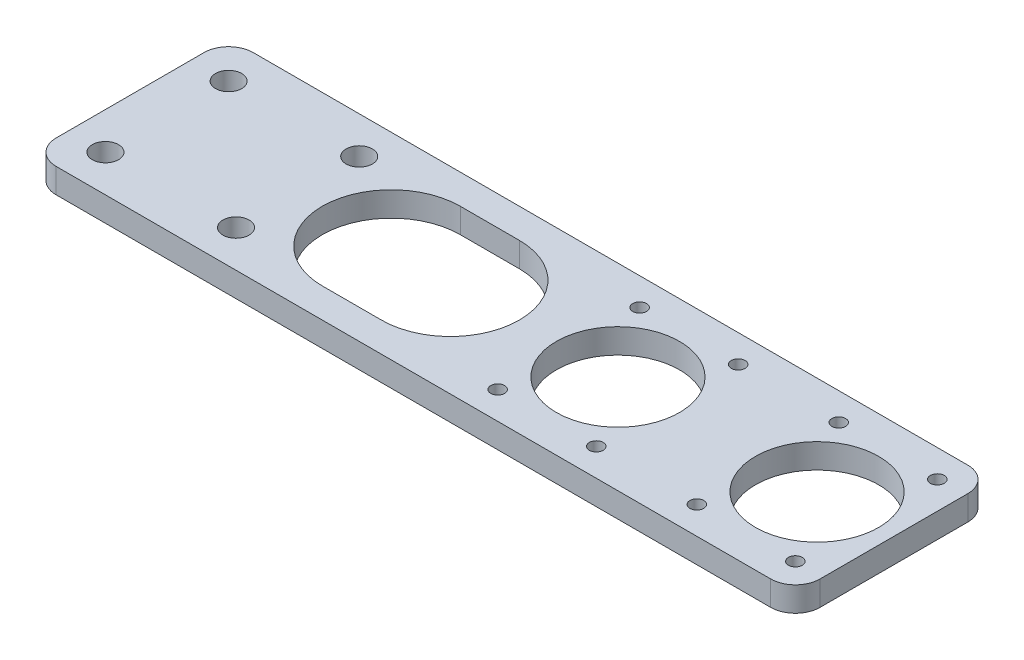
SolidWorks part; units mm, degrees
material "6061-T6 (SS)"
ref_plane "Front Plane" through (0, 0, 0) normal (0, 0, 1) x (1, 0, 0)
ref_plane "Top Plane" through (0, 0, 0) normal (0, 1, 0) x (1, 0, 0)
ref_plane "Right Plane" through (0, 0, 0) normal (1, 0, 0) x (0, 0, -1)
sketch "Sketch1" plane through (0, 0, 0) normal (0, 1, 0) x (1, 0, 0)
  line L0 (-113.03, 25.4) -> (-113.03, -25.4)
  line L1 (-113.03, 25.4) -> (77.47, 25.4)
  line L3 (-113.03, -25.4) -> (77.47, -25.4)
  line L4 (83.82, 19.05) -> (83.82, -19.05)
  line L7 (-45.72, 0) -> (12.7, 0) construction
  line L8 (12.7, 0) -> (64.008, 0) construction
  line L9 (0, 18.288) -> (92.5107, 18.288) construction
  line L12 (0, -18.288) -> (104.0184, -18.288) construction
  line L18 (-30.48, 17.78) -> (-45.72, 17.78)
  line L19 (-30.48, -17.78) -> (-45.72, -17.78)
  arc A0 (-45.72, 17.78) -> (-45.72, -17.78) centre (-45.72, 0) ccw
  arc A5 (77.47, -25.4) -> (83.82, -19.05) centre (77.47, -19.05) ccw
  arc A6 (77.47, 25.4) -> (83.82, 19.05) centre (77.47, 19.05) cw
  circle A11 centre (12.7, 0) radius 15.875
  circle A12 centre (64.008, 0) radius 15.875
  circle A13 centre (0, 18.288) radius 1.778
  circle A14 centre (25.4, 18.288) radius 1.778
  circle A15 centre (51.308, 18.288) radius 1.778
  circle A16 centre (76.708, 18.288) radius 1.778
  circle A17 centre (0, -18.288) radius 1.778
  circle A18 centre (25.4, -18.288) radius 1.778
  circle A19 centre (51.308, -18.288) radius 1.778
  circle A20 centre (76.708, -18.288) radius 1.778
  arc A23 (-30.48, -17.78) -> (-30.48, 17.78) centre (-30.48, 0) ccw
  point P0 (0, 0)
  dimension "D4" = 25.4
  dimension "D14" = 6.35
  dimension "D7" = 31.75
  dimension "D8" = 31.75
  dimension "D9" = 3.556
  dimension "D10" = 36.576
  dimension "D15" = 18.288
  dimension "D16" = 0
  dimension "D17" = 0
  dimension "D18" = 0
  dimension "D19" = 0
  dimension "D20" = 0
  dimension "D21" = 0
  dimension "D22" = 12.7
  dimension "D23" = 12.7
  dimension "D24" = 12.7
  dimension "D25" = 12.7
  dimension "D26" = 12.7
  dimension "D27" = 12.7
  dimension "D28" = 12.7
  dimension "D29" = 12.7
  dimension "D30" = 45.72
  dimension "D32" = 17.78
  dimension "D33" = 17.78
  dimension "D31" = 15.24
  dimension "D5" = 58.42
  dimension "D6" = 51.308
  dimension "D11" = 25.4
  dimension "D12" = 190.5
  dimension "D13" = 190.5
  dimension "D35" = 83.82
extrude "Boss-Extrude1" add sketch "Sketch1" along normal blind 6.35
sketch "Sketch5" plane through (0, 6.35, 0) normal (0, 1, 0) x (1, 0, 0)
  line L0 (-63.5, 0) -> (-113.03, 0) construction
  line L1 (-113.03, 25.4) -> (-113.03, -25.4) construction
  line L2 (-113.03, 15.875) -> (-57.4608, 15.875) construction
  line L3 (-113.03, -15.875) -> (-60.8112, -15.875) construction
  line L4 (-103.505, 25.4) -> (-103.505, -38.1981) construction
  line L5 (77.47, 25.4) -> (-113.03, 25.4) construction
  line L6 (-69.85, -32.8742) -> (-69.85, 30.7239) construction
  arc A0 (-45.72, 17.78) -> (-45.72, -17.78) centre (-45.72, 0) ccw construction
  dimension "D1" = 15.875
  dimension "D2" = 15.875
  dimension "D3" = 9.525
  dimension "D4" = 6.35
hole_wizard "1/4 Clearance Hole2" positions "Sketch6" profile "Sketch7" hole size "1/4" standard "ANSI Inch" end condition up to next
sketch "Sketch6" plane through (0, 6.35, 0) normal (0, 1, 0) x (1, 0, 0)
  line L0 (-113.03, 15.875) -> (-57.4608, 15.875) construction
  line L1 (-103.505, 25.4) -> (-103.505, -38.1981) construction
  line L2 (-69.85, -32.8742) -> (-69.85, 30.7239) construction
  line L3 (-113.03, -15.875) -> (-60.8112, -15.875) construction
  point P0 (-103.505, 15.875)
  point P6 (-69.85, 15.875)
  point P10 (-69.85, -15.875)
  point P14 (-103.505, -15.875)
sketch "Sketch7" plane through (-103.505, 6.35, -15.875) normal (1, 0, 0) x (0, 0, 1)
  line L0 (0, 0) -> (0, 6.35)
  line L1 (0, 6.35) -> (3.3782, 6.35)
  line L2 (3.3782, 6.35) -> (3.3782, 0)
  line L5 (3.3782, 0) -> (0, 0)
  line L11 (0, -6.35) -> (0, 107.95) construction
  dimension "Thru Hole Dia." = 6.7564
  dimension "Thru Hole Depth" = 6.35
fillet "Fillet1" radius 6.35 2 edges at (-113.03, 3.175, 25.4) (-113.03, 3.175, -25.4)
